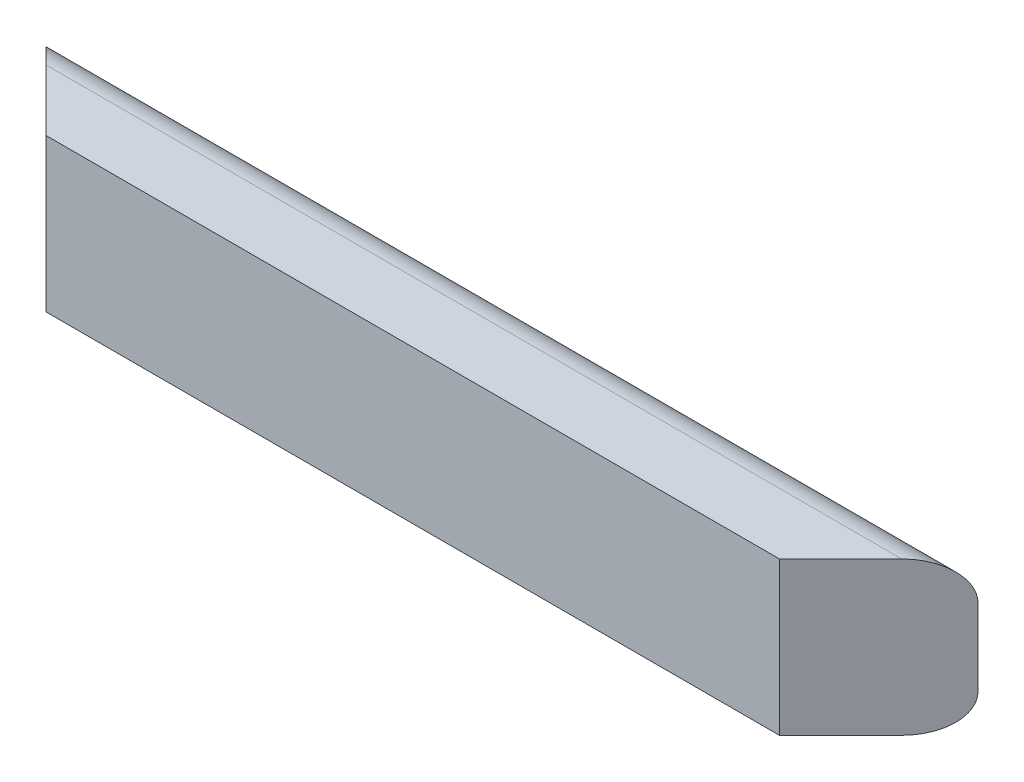
SolidWorks part; units mm, degrees
ref_plane "Front" through (0, 0, 0) normal (0, 0, 1) x (1, 0, 0)
ref_plane "Top" through (0, 0, 0) normal (0, 1, 0) x (1, 0, 0)
ref_plane "Right" through (0, 0, 0) normal (1, 0, 0) x (0, 0, -1)
sketch "Sketch1" plane through (0, 0, 0) normal (1, 0, 0) x (0, 0, -1)
  line L0 (0, 0) -> (0, 127) construction
  line L1 (0, 0) -> (31.75, 0)
  line L2 (31.75, 127) -> (0, 127)
  line L3 (63.5, 95.25) -> (63.5, 31.75)
  line L4 (0, 0) -> (-19.05, 0)
  line L5 (-19.05, 0) -> (-19.05, 127)
  line L6 (-19.05, 127) -> (0, 127)
  arc A0 (31.75, 0) -> (63.5, 31.75) centre (31.75, 31.75) ccw
  arc A1 (63.5, 95.25) -> (31.75, 127) centre (31.75, 95.25) ccw
  dimension "D2" = 63.5
  dimension "D1" = 19.05
extrude "Boss-Extrude1" add sketch "Sketch1" along normal blind 774.7
ref_plane "Mid_Plane" through (387.35, 0, 0) normal (1, 0, 0) x (0, 0, -1)
ref_plane "Plane1" through (355.6, 0, 355.6) normal (0.7071, 0, 0.7071) x (0, 1, 0)
sketch "Sketch2" plane through (355.6, 0, 355.6) normal (0.7071, 0, 0.7071) x (0, 1, 0)
  line L0 (31.75, -592.6969) -> (95.25, -592.6969) construction
  line L1 (205.1964, -202.4681) -> (-139.2061, -202.4681)
  line L2 (205.1964, -202.4681) -> (205.1964, -982.9257)
  line L3 (205.1964, -982.9257) -> (-139.2061, -982.9257)
  line L4 (-139.2061, -202.4681) -> (-139.2061, -982.9257)
  line L5 (205.1964, -202.4681) -> (-139.2061, -982.9257) construction
  line L6 (205.1964, -982.9257) -> (-139.2061, -202.4681) construction
  point P4 (32.9952, -592.6969)
extrude "Cut-Extrude1" cut sketch "Sketch2" along normal through all
mirror "Mirror1" about plane through (387.35, 0, 0) normal (1, 0, 0) of "Cut-Extrude1"
